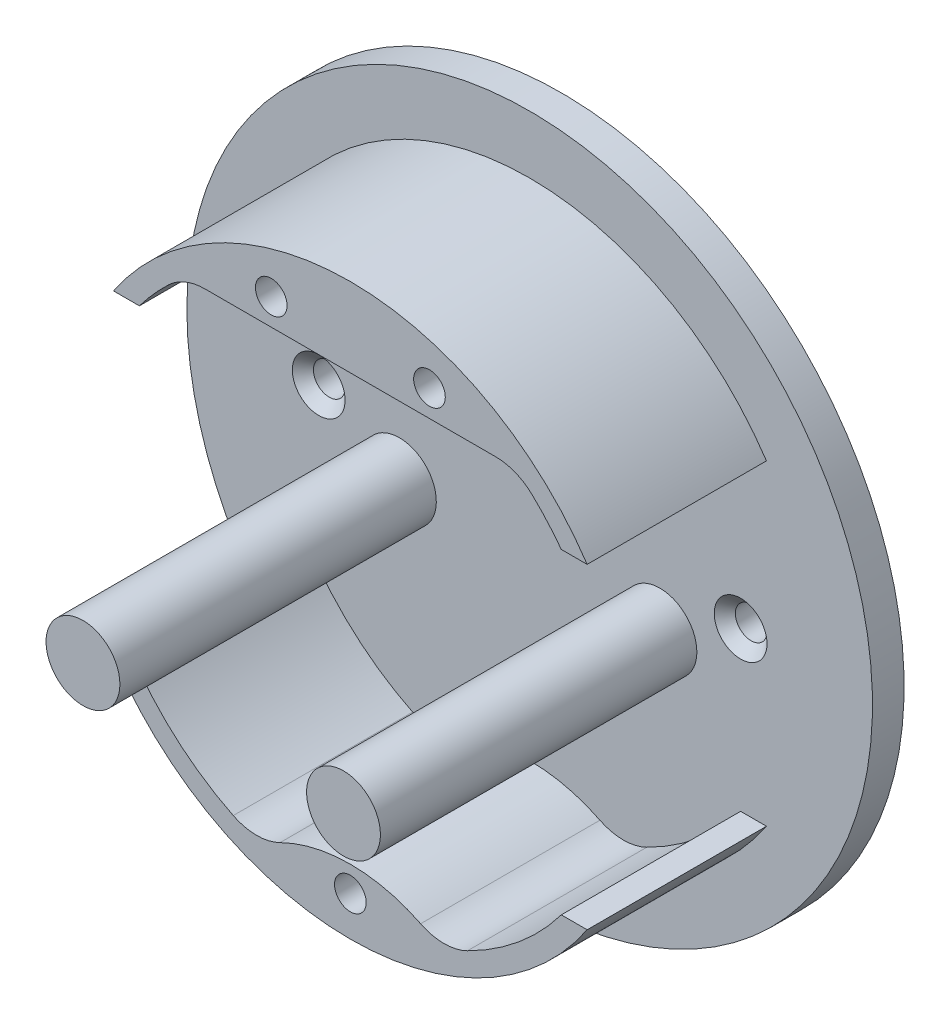
SolidWorks part; units mm, degrees
ref_plane "Front Plane" through (0, 0, 0) normal (0, 0, 1) x (1, 0, 0)
ref_plane "Top Plane" through (0, 0, 0) normal (0, 1, 0) x (1, 0, 0)
ref_plane "Right Plane" through (0, 0, 0) normal (1, 0, 0) x (0, 0, -1)
sketch "Sketch3" plane through (0, 0, 0) normal (0, 0, 1) x (1, 0, 0)
  circle A0 centre (0, 0) radius 27
  circle A1 centre (0, 0) radius 25
  dimension "D1" = 54
  dimension "D2" = 50
extrude "Boss-Extrude2" add sketch "Sketch3" along normal blind 20
sketch "Sketch4" plane through (0, 0, 0) normal (1, 0, 0) x (0, 0, -1)
  line L1 (-24.3949, 15) -> (-3, 15)
  line L2 (-24.3949, 15) -> (-24.3949, -15)
  line L3 (-24.3949, -15) -> (-3, -15)
  line L4 (-3, 15) -> (-3, -15)
  dimension "D1" = 15
  dimension "D2" = 30
  dimension "D3" = 3
extrude "Cut-Extrude1" cut sketch "Sketch4" against normal through all both and the other way through all
sketch "Sketch5" plane through (0, 0, 0) normal (0, 0, 1) x (1, 0, 0)
  line L0 (-15.6445, 19.5) -> (15.6445, 19.5)
  circle A1 centre (0, -23.25) radius 1.5
  circle A2 centre (-7.5, 22.0071) radius 1.5
  circle A3 centre (7.5, 22.0071) radius 1.5
  arc A4 (20, 15) -> (-20, 15) centre (0, 0) ccw construction
  arc A5 (-15.6445, 19.5) -> (15.6445, 19.5) centre (0, 4.8656) cw
  arc A6 (8.5294, -23.5) -> (-8.5294, -23.5) centre (0, -35.839) ccw
  arc A7 (-20, -15) -> (20, -15) centre (0, 0) ccw construction
  arc A8 (-8.5294, -23.5) -> (8.5294, -23.5) centre (0, -11.4252) ccw
  dimension "D1" = 15
  dimension "D2" = 7.5
  dimension "D3" = 23.25
  dimension "D4" = 15
  dimension "D5" = 3
  dimension "D6" = 3
  dimension "D7" = 23.25
  dimension "D8" = 3
  dimension "D9" = 23.25
  dimension "D10" = 19.5
extrude "Boss-Extrude3" add sketch "Sketch5" along normal blind 20
fillet "Fillet2" radius 5 4 edges at (-8.5294, -23.5, 10) (8.5294, -23.5, 10) (15.6445, 19.5, 10) (-15.6445, 19.5, 10)
sketch "Sketch6" plane through (0, 0, 0) normal (0, 0, -1) x (-1, 0, 0)
  circle A0 centre (0, 0) radius 32.5
  dimension "D1" = 65
extrude "Boss-Extrude4" add sketch "Sketch6" against normal blind 3
sketch "Sketch7" plane through (0, 0, 3) normal (0, 0, 1) x (1, 0, 0)
  circle A0 centre (0, 15) radius 4
  dimension "D1" = 8
  dimension "D2" = 15
extrude "Cut-Extrude2" cut sketch "Sketch7" against normal through all
sketch "Sketch8" plane through (0, 0, 3) normal (0, 0, 1) x (1, 0, 0)
  circle A0 centre (-20, 0) radius 1.5
  circle A1 centre (20, 0) radius 1.5
  dimension "D1" = 3
  dimension "D2" = 20
  dimension "D3" = 3
  dimension "D4" = 20
extrude "Cut-Extrude3" cut sketch "Sketch8" against normal through all
chamfer "Chamfer1" distance 1 angle 45 2 edges at (21.5, 0, 3) (-18.5, 0, 3)
sketch "Sketch9" plane through (0, 0, 3) normal (0, 0, 1) x (1, 0, 0)
  circle A0 centre (-12.35, -4) radius 3.5
  circle A1 centre (12.35, -4) radius 3.5
  dimension "D1" = 7
  dimension "D2" = 7
  dimension "D3" = 24.7
  dimension "D4" = 12.35
  dimension "D5" = 4
extrude "Boss-Extrude5" add sketch "Sketch9" along normal blind 30
